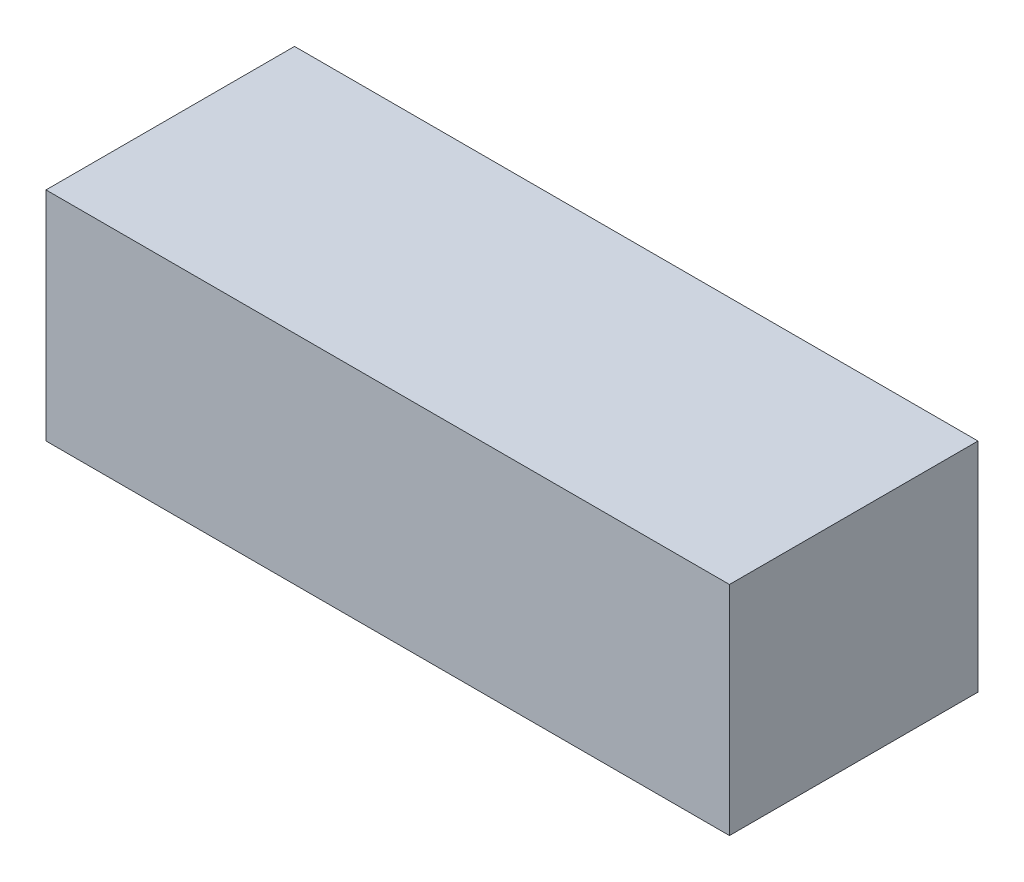
SolidWorks part; units mm, degrees
ref_plane "Front Plane" through (0, 0, 0) normal (0, 0, 1) x (1, 0, 0)
ref_plane "Top Plane" through (0, 0, 0) normal (0, 1, 0) x (1, 0, 0)
ref_plane "Right Plane" through (0, 0, 0) normal (1, 0, 0) x (0, 0, -1)
sketch "Sketch1" plane through (0, 0, 0) normal (0, 1, 0) x (1, 0, 0)
  line L1 (-22, -8) -> (22, -8)
  line L2 (-22, -8) -> (-22, 8)
  line L3 (-22, 8) -> (22, 8)
  line L4 (22, -8) -> (22, 8)
  line L5 (-22, -8) -> (22, 8) construction
  line L6 (-22, 8) -> (22, -8) construction
  point P0 (0, 0)
  dimension "D1" = 16
  dimension "D2" = 44
extrude "Boss-Extrude1" add sketch "Sketch1" along normal blind 14
